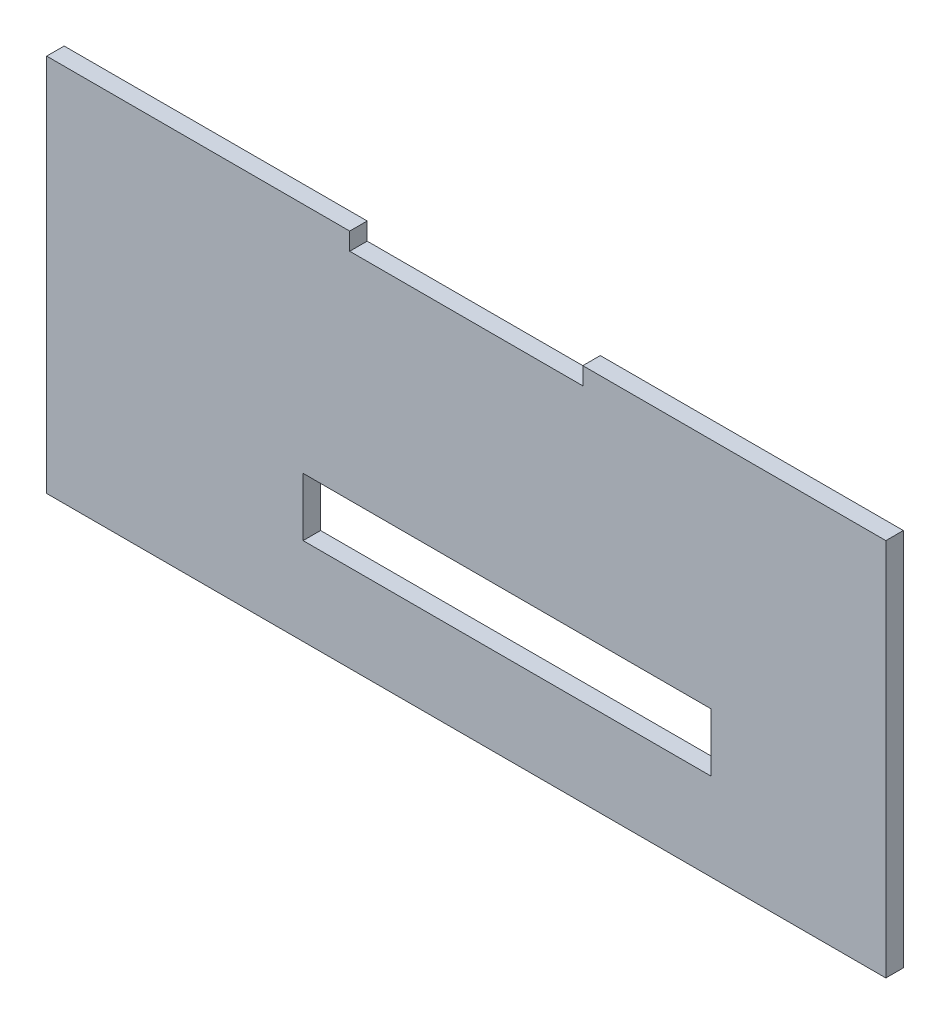
SolidWorks part; units mm, degrees
ref_plane "Plano frontal" through (0, 0, 0) normal (0, 0, 1) x (1, 0, 0)
ref_plane "Plano superior" through (0, 0, 0) normal (0, 1, 0) x (1, 0, 0)
ref_plane "Plano direito" through (0, 0, 0) normal (1, 0, 0) x (0, 0, -1)
sketch "Esboço1" plane through (0, 0, 0) normal (0, 0, 1) x (1, 0, 0)
  line L0 (-120.2864, 37.2829) -> (23.7136, 37.2829)
  line L1 (-120.2864, 37.2829) -> (-120.2864, -27.7171)
  line L2 (-120.2864, -27.7171) -> (23.7136, -27.7171)
  line L3 (23.7136, 37.2829) -> (23.7136, -27.7171)
  line L4 (-76.2864, -2.7171) -> (-6.2864, -2.7171)
  line L5 (-76.2864, -2.7171) -> (-76.2864, -12.7171)
  line L6 (-76.2864, -12.7171) -> (-6.2864, -12.7171)
  line L7 (-6.2864, -2.7171) -> (-6.2864, -12.7171)
  line L8 (-68.2864, 37.2829) -> (-28.2864, 37.2829)
  line L9 (-68.2864, 37.2829) -> (-68.2864, 34.2829)
  line L10 (-68.2864, 34.2829) -> (-28.2864, 34.2829)
  line L11 (-28.2864, 37.2829) -> (-28.2864, 34.2829)
  dimension "D1" = 25
  dimension "D2" = 30
  dimension "D3" = 144
  dimension "D4" = 70
  dimension "D5" = 10
  dimension "D6" = 0
  dimension "D7" = 40
  dimension "D8" = 52
  dimension "D9" = 52
  dimension "D10" = 3
  dimension "D11" = 65
extrude "Ressalto-extrusão1" add sketch "Esboço1" against normal blind 2 and the other way blind 1 contours L0 L11 L10 L9 L1 L2 L3 L4 L7 L6 L5
